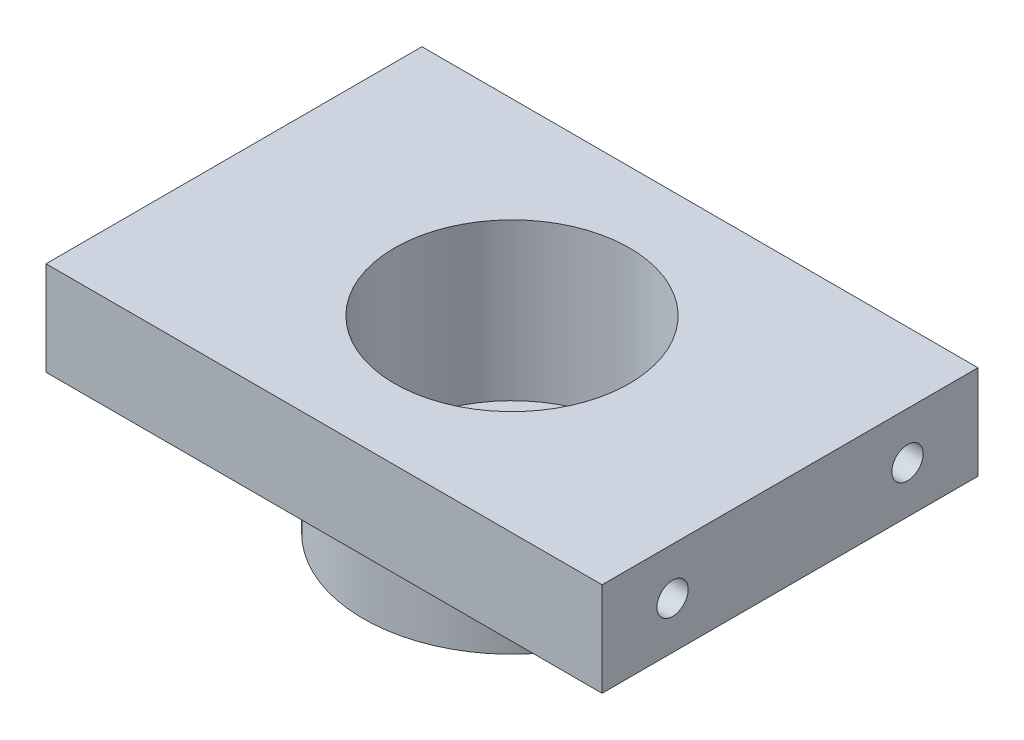
SolidWorks part; units mm, degrees
ref_plane "Plan de face" through (0, 0, 0) normal (0, 0, 1) x (1, 0, 0)
ref_plane "Plan de dessus" through (0, 0, 0) normal (0, 1, 0) x (1, 0, 0)
ref_plane "Plan de droite" through (0, 0, 0) normal (1, 0, 0) x (0, 0, -1)
sketch "Esquisse1" plane through (0, 0, 0) normal (0, 0, 1) x (1, 0, 0)
  line L0 (0, 0) -> (0, -20) construction
  line L1 (19, -12) -> (59, -12)
  line L2 (15, -20) -> (15, 0)
  line L3 (15, -20) -> (9, -20)
  line L5 (59, 0) -> (59, -12)
  line L6 (9, -24) -> (19, -24)
  line L7 (9, -20) -> (9, -24)
  line L9 (19, -24) -> (19, -12)
  line L10 (59, 0) -> (15, 0)
  dimension "D1" = 20
  dimension "D2" = 10
  dimension "D3" = 6
  dimension "D4" = 9
  dimension "D5" = 59
  dimension "D6" = 12
  dimension "D7" = 12
revolve "Révolution1" add sketch "Esquisse1" angle 360 about L0
sketch "Esquisse4" plane through (0, -24, 0) normal (0, -1, 0) x (1, 0, 0)
  line L0 (0, 0) -> (0, 13) construction
  circle A0 centre (0, 13) radius 1.5
  circle A1 centre (13, 0) radius 1.5
  circle A2 centre (0, -13) radius 1.5
  circle A3 centre (-13, 0) radius 1.5
  dimension "D1" = 3
  dimension "D2" = 13
  dimension "D3" = 13
  dimension "D4" = 13
extrude "Extrusion3" cut sketch "Esquisse4" against normal through all
sketch "Esquisse5" plane through (0, -12, 0) normal (0, -1, 0) x (1, 0, 0)
  line L0 (0, 13) -> (13, 0) construction
  line L1 (0, 0) -> (-35.5, 0) construction
  line L2 (-35.5, -24) -> (-35.5, 24)
  line L3 (0, 0) -> (0, -24) construction
  line L4 (35.5, -24) -> (35.5, 24)
  line L5 (35.5, 24) -> (-35.5, 24)
  line L6 (35.5, -24) -> (-35.5, -24)
  dimension "D1" = 48
  dimension "D2" = 71
  dimension "D3" = 35.5
extrude "Extrusion4" cut sketch "Esquisse5" against normal through all flip side to cut
sketch "Esquisse6" plane through (35.5, 0, 0) normal (1, 0, 0) x (0, 0, -1)
  line L0 (-24, -6) -> (24, -6) construction
  line L1 (-24, 0) -> (-24, -12) construction
  line L2 (24, 0) -> (24, -12) construction
  line L3 (0, -12) -> (0, 0) construction
  line L4 (24, -12) -> (-24, -12) construction
  line L5 (24, 0) -> (-24, 0) construction
  circle A0 centre (-15, -6) radius 2
  circle A1 centre (15, -6) radius 2
  dimension "D1" = 4
  dimension "D2" = 9
extrude "Extrusion5" cut sketch "Esquisse6" against normal blind 10
sketch "Esquisse7" plane through (-35.5, 0, 0) normal (-1, 0, 0) x (0, 0, 1)
  line L0 (24, -6) -> (-24, -6) construction
  line L1 (24, 0) -> (24, -12) construction
  line L2 (-24, 0) -> (-24, -12) construction
  line L3 (0, 0) -> (0, -12) construction
  line L6 (24, -12) -> (-24, -12) construction
  circle A0 centre (15, -6) radius 2
  circle A1 centre (15, -6) radius 2 construction
  circle A2 centre (-15, -6) radius 2
extrude "Extrusion6" cut sketch "Esquisse7" against normal blind 10
